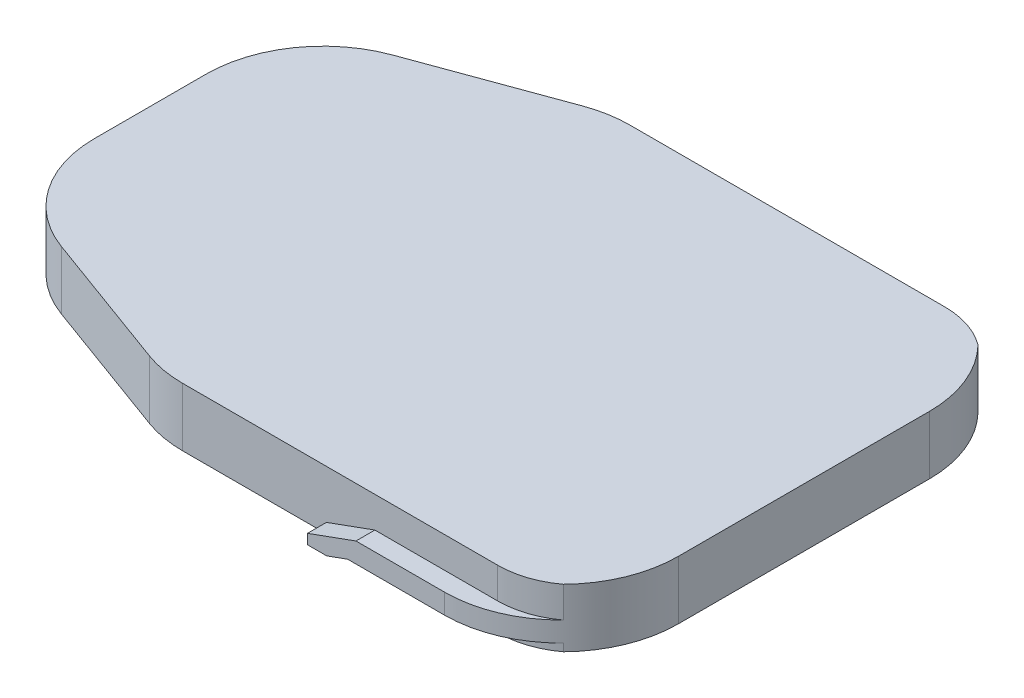
SolidWorks part; units mm, degrees
ref_plane "前视基准面" through (0, 0, 0) normal (0, 0, 1) x (1, 0, 0)
ref_plane "上视基准面" through (0, 0, 0) normal (0, 1, 0) x (1, 0, 0)
ref_plane "右视基准面" through (0, 0, 0) normal (1, 0, 0) x (0, 0, -1)
other "Configuration Table"
sketch "草图1" plane through (0, 0, 0) normal (0, 1, 0) x (1, 0, 0)
  line L0 (-47.5, 20) -> (-13.3, 32.5)
  line L1 (47.5, -32.5) -> (-13.3, -32.5)
  line L2 (47.5, -32.5) -> (47.5, 32.5)
  line L3 (47.5, 32.5) -> (-13.3, 32.5)
  line L4 (-47.5, -20) -> (-47.5, 20)
  line L5 (47.5, -32.5) -> (-35.5919, 24.3524) construction
  line L6 (47.5, 32.5) -> (-35.5919, -24.3524) construction
  line L7 (-47.5, -20) -> (-13.3, -32.5)
  point P0 (0, 0)
  dimension "D1" = 95
  dimension "D2" = 65
  dimension "D3" = 40
  dimension "D4" = 12.5
  dimension "D5" = 34.2
  dimension "D6" = 34.2
  dimension "D7" = 47.5
  dimension "D8" = 32.5
extrude "凸台-拉伸1" add sketch "草图1" along normal blind 8.5
sketch "草图3" plane through (0, 0, 0) normal (0, -1, 0) x (1, 0, 0)
  line L0 (47.5, 32.5) -> (47.5, -32.5) construction
  line L1 (-13.3, 32.5) -> (47.5, 32.5) construction
  line L2 (-47.5, 0) -> (47.5, 0) construction
  line L3 (-47.5, -20) -> (-47.5, 20) construction
  line L4 (-12.6, -15.65) -> (20.1, -15.65) construction
  line L9 (-12.6, 15.65) -> (20.1, 15.65) construction
  line L10 (-12.6, 29.55) -> (20.1, 29.55)
  line L11 (-12.6, 1.75) -> (20.1, 1.75)
  line L12 (-12.6, -29.55) -> (20.1, -29.55)
  line L13 (-12.6, -1.75) -> (20.1, -1.75)
  arc A4 (-12.6, 29.55) -> (-12.6, 1.75) centre (-12.6, 15.65) ccw
  arc A5 (20.1, 1.75) -> (20.1, 29.55) centre (20.1, 15.65) ccw
  arc A6 (-12.6, -29.55) -> (-12.6, -1.75) centre (-12.6, -15.65) cw
  arc A7 (20.1, -1.75) -> (20.1, -29.55) centre (20.1, -15.65) cw
  point P4 (3.75, 15.65)
  point P17 (3.75, -15.65)
  dimension "D1" = 43.75
  dimension "D4" = 2.95
  dimension "D2" = 27.8
  dimension "D3" = 27.4
extrude "切除-拉伸1" cut sketch "草图3" against normal blind 3.4
sketch "草图7" plane through (0, 3.4, 0) normal (0, -1, 0) x (1, 0, 0)
  line L0 (-26.5, 15.65) -> (34, 15.65) construction
  line L1 (3.75, 29.55) -> (3.75, 1.75) construction
  line L2 (20.1, 29.55) -> (-12.6, 29.55) construction
  line L3 (-12.6, 1.75) -> (20.1, 1.75) construction
  line L4 (-13.3, 32.5) -> (47.5, 32.5) construction
  line L5 (2, 29.55) -> (5.5, 29.55)
  line L6 (2, 29.55) -> (2, 24.5)
  line L7 (2, 24.5) -> (5.5, 24.5)
  line L8 (5.5, 29.55) -> (5.5, 24.5)
  arc A0 (-12.6, 29.55) -> (-12.6, 1.75) centre (-12.6, 15.65) ccw construction
  arc A1 (20.1, 1.75) -> (20.1, 29.55) centre (20.1, 15.65) ccw construction
  dimension "D1" = 8
  dimension "D2" = 3.5
  dimension "D3" = 1.75
extrude "凸台-拉伸2" add sketch "草图7" along normal up to surface (3.4 mm away) up to face at (3.75, 0, 15.65)
mirror "镜向1" about plane through (0, 0, 0) normal (0, 0, 1) of "凸台-拉伸2"
sketch "草图8" plane through (0, 0, 0) normal (0, -1, 0) x (1, 0, 0)
  line L0 (-12.6, 1.75) -> (20.1, 1.75) construction
  line L1 (0, 1.75) -> (7.5, 1.75)
  line L2 (0, 1.75) -> (0, -1.75)
  line L3 (0, -1.75) -> (7.5, -1.75)
  line L4 (7.5, 1.75) -> (7.5, -1.75)
  line L5 (20.1, -1.75) -> (-12.6, -1.75) construction
  line L6 (47.5, 32.5) -> (47.5, -32.5) construction
  dimension "D1" = 40
  dimension "D2" = 7.5
extrude "切除-拉伸2" cut sketch "草图8" against normal blind 3
sketch "草图10" plane through (0, 0, 32.5) normal (0, 0, 1) x (1, 0, 0)
  line L0 (16.4297, 1.1) -> (47.5, 1.1)
  line L1 (17.6424, 4) -> (47.5, 4)
  line L2 (10.6, 1.4416) -> (10.6, 0)
  line L3 (10.6, 0) -> (13.4018, 0)
  line L4 (47.5, 4) -> (47.5, 1.1)
  line L5 (10.6, 1.4416) -> (17.6424, 4)
  line L6 (13.4018, 0) -> (16.4297, 1.1)
  line L7 (-13.3, 0) -> (47.5, 0) construction
  line L9 (-47.5, 8.5) -> (-47.5, 0) construction
  dimension "D1" = 2.8018
  dimension "D2" = 31.0703
  dimension "D3" = 2.9
  dimension "D4" = 180
  dimension "D5" = 7.0424
  dimension "D6" = 1.4416
  dimension "D7" = 29.8576
  dimension "D8" = 1.1
  dimension "D9" = 95
extrude "凸台-拉伸3" add sketch "草图10" along normal blind 2.75
mirror "镜向2" about plane through (0, 0, 0) normal (0, 0, 1) of "凸台-拉伸3"
fillet "圆角2" radius 12 4 edges at (47.5, 0.55, 32.5) (47.5, 6.25, 32.5) (47.5, 0.55, -32.5) (47.5, 6.25, -32.5)
fillet "圆角3" radius 17 2 edges at (47.5, 2.55, 35.25) (47.5, 2.55, -35.25)
fillet "圆角4" radius 17 4 edges at (-47.5, 4.25, 20) (-47.5, 4.25, -20) (-13.3, 4.25, -32.5) (-13.3, 4.25, 32.5)
